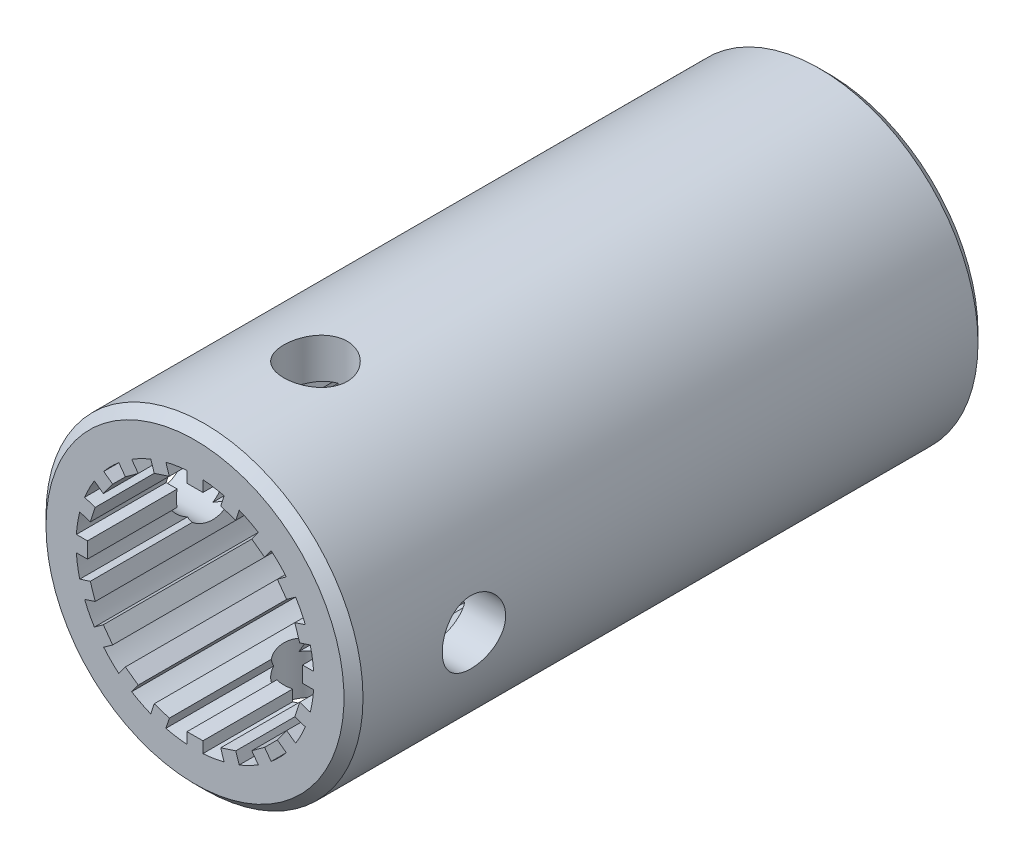
SolidWorks part; units mm, degrees
material "Plain Carbon Steel"
ref_plane "Front Plane" through (0, 0, 0) normal (0, 0, 1) x (1, 0, 0)
ref_plane "Top Plane" through (0, 0, 0) normal (0, 1, 0) x (1, 0, 0)
ref_plane "Right Plane" through (0, 0, 0) normal (1, 0, 0) x (0, 0, -1)
sketch "Sketch1" plane through (0, 0, 0) normal (1, 0, 0) x (0, 0, -1)
  line L0 (-58.8777, 0) -> (63.6887, 0) construction
  line L1 (-25.4, 0) -> (-25.4, 12.7)
  line L2 (-25.4, 12.7) -> (25.4, 12.7)
  line L3 (25.4, 12.7) -> (25.4, 0)
  line L4 (-25.4, 0) -> (25.4, 0)
  point P5 (0, 12.7)
  dimension "D1" = 50.8
  dimension "D2" = 12.7
revolve "Revolve1" add sketch "Sketch1" angle 360 about L0
sketch "Sketch2" plane through (0, 0, 0) normal (0, 1, 0) x (1, 0, 0)
  line L0 (0, 0) -> (0, 50000) construction
  line L1 (-12.7, -25.4) -> (12.7, -25.4) construction
  line L2 (-12.7, -25.4) -> (12.7, -25.4) construction
  circle A0 centre (0, -15.748) radius 2.54
  dimension "D1" = 5.08
  dimension "D2" = 9.652
extrude "Cut-Extrude1" cut sketch "Sketch2" against normal mid plane 34.798
sketch "Sketch3" plane through (0, 0, 0) normal (1, 0, 0) x (0, 0, -1)
  line L0 (0, 0) -> (-50000, 0) construction
  line L1 (-25.4, 12.7) -> (-25.4, -12.7) construction
  line L2 (-25.4, 12.7) -> (-25.4, -12.7) construction
  circle A0 centre (-15.748, 0) radius 2.54
  dimension "D1" = 5.08
  dimension "D2" = 9.652
extrude "Cut-Extrude2" cut sketch "Sketch3" against normal mid plane 34.798
sketch "Sketch4" plane through (0, 0, 25.4) normal (0, 0, 1) x (1, 0, 0)
  line L0 (0, 0) -> (0, 10.781) construction
  line L1 (-0.635, 8.6148) -> (0.635, 8.6148)
  line L2 (0.635, 8.6148) -> (0.635, 9.5038)
  line L3 (-0.635, 8.6148) -> (-0.635, 9.5038)
  line L4 (2.0582, 8.3894) -> (2.3329, 9.2349)
  line L5 (2.0582, 8.3894) -> (3.266, 7.9969)
  line L6 (3.266, 7.9969) -> (3.5408, 8.8424)
  line L7 (4.5499, 7.3428) -> (5.0725, 8.062)
  line L8 (4.5499, 7.3428) -> (5.5774, 6.5963)
  line L9 (5.5774, 6.5963) -> (6.0999, 7.3155)
  line L10 (6.5963, 5.5774) -> (7.3155, 6.0999)
  line L11 (6.5963, 5.5774) -> (7.3428, 4.5499)
  line L12 (7.3428, 4.5499) -> (8.062, 5.0725)
  line L13 (7.9969, 3.266) -> (8.8424, 3.5408)
  line L14 (7.9969, 3.266) -> (8.3894, 2.0582)
  line L15 (8.3894, 2.0582) -> (9.2349, 2.3329)
  line L16 (8.6148, 0.635) -> (9.5038, 0.635)
  line L17 (8.6148, 0.635) -> (8.6148, -0.635)
  line L18 (8.6148, -0.635) -> (9.5038, -0.635)
  line L19 (8.3894, -2.0582) -> (9.2349, -2.3329)
  line L20 (8.3894, -2.0582) -> (7.9969, -3.266)
  line L21 (7.9969, -3.266) -> (8.8424, -3.5408)
  line L22 (7.3428, -4.5499) -> (8.062, -5.0725)
  line L23 (7.3428, -4.5499) -> (6.5963, -5.5774)
  line L24 (6.5963, -5.5774) -> (7.3155, -6.0999)
  line L25 (5.5774, -6.5963) -> (6.0999, -7.3155)
  line L26 (5.5774, -6.5963) -> (4.5499, -7.3428)
  line L27 (4.5499, -7.3428) -> (5.0725, -8.062)
  line L28 (3.266, -7.9969) -> (3.5408, -8.8424)
  line L29 (3.266, -7.9969) -> (2.0582, -8.3894)
  line L30 (2.0582, -8.3894) -> (2.3329, -9.2349)
  line L31 (0.635, -8.6148) -> (0.635, -9.5038)
  line L32 (0.635, -8.6148) -> (-0.635, -8.6148)
  line L33 (-0.635, -8.6148) -> (-0.635, -9.5038)
  line L34 (-2.0582, -8.3894) -> (-2.3329, -9.2349)
  line L35 (-2.0582, -8.3894) -> (-3.266, -7.9969)
  line L36 (-3.266, -7.9969) -> (-3.5408, -8.8424)
  line L37 (-4.5499, -7.3428) -> (-5.0725, -8.062)
  line L38 (-4.5499, -7.3428) -> (-5.5774, -6.5963)
  line L39 (-5.5774, -6.5963) -> (-6.0999, -7.3155)
  line L40 (-6.5963, -5.5774) -> (-7.3155, -6.0999)
  line L41 (-6.5963, -5.5774) -> (-7.3428, -4.5499)
  line L42 (-7.3428, -4.5499) -> (-8.062, -5.0725)
  line L43 (-7.9969, -3.266) -> (-8.8424, -3.5408)
  line L44 (-7.9969, -3.266) -> (-8.3894, -2.0582)
  line L45 (-8.3894, -2.0582) -> (-9.2349, -2.3329)
  line L46 (-8.6148, -0.635) -> (-9.5038, -0.635)
  line L47 (-8.6148, -0.635) -> (-8.6148, 0.635)
  line L48 (-8.6148, 0.635) -> (-9.5038, 0.635)
  line L49 (-8.3894, 2.0582) -> (-9.2349, 2.3329)
  line L50 (-8.3894, 2.0582) -> (-7.9969, 3.266)
  line L51 (-7.9969, 3.266) -> (-8.8424, 3.5408)
  line L52 (-7.3428, 4.5499) -> (-8.062, 5.0725)
  line L53 (-7.3428, 4.5499) -> (-6.5963, 5.5774)
  line L54 (-6.5963, 5.5774) -> (-7.3155, 6.0999)
  line L55 (-5.5774, 6.5963) -> (-6.0999, 7.3155)
  line L56 (-5.5774, 6.5963) -> (-4.5499, 7.3428)
  line L57 (-4.5499, 7.3428) -> (-5.0725, 8.062)
  line L58 (-3.266, 7.9969) -> (-3.5408, 8.8424)
  line L59 (-3.266, 7.9969) -> (-2.0582, 8.3894)
  line L60 (-2.0582, 8.3894) -> (-2.3329, 9.2349)
  arc A0 (-3.5408, 8.8424) -> (-5.0725, 8.062) centre (0, 0) ccw
  arc A1 (-6.0999, 7.3155) -> (-7.3155, 6.0999) centre (0, 0) ccw
  arc A2 (-8.062, 5.0725) -> (-8.8424, 3.5408) centre (0, 0) ccw
  arc A3 (-9.2349, 2.3329) -> (-9.5038, 0.635) centre (0, 0) ccw
  arc A4 (-9.5038, -0.635) -> (-9.2349, -2.3329) centre (0, 0) ccw
  arc A5 (-8.8424, -3.5408) -> (-8.062, -5.0725) centre (0, 0) ccw
  arc A6 (-7.3155, -6.0999) -> (-6.0999, -7.3155) centre (0, 0) ccw
  arc A7 (-5.0725, -8.062) -> (-3.5408, -8.8424) centre (0, 0) ccw
  arc A8 (-2.3329, -9.2349) -> (-0.635, -9.5038) centre (0, 0) ccw
  arc A9 (0.635, -9.5038) -> (2.3329, -9.2349) centre (0, 0) ccw
  arc A10 (3.5408, -8.8424) -> (5.0725, -8.062) centre (0, 0) ccw
  arc A11 (6.0999, -7.3155) -> (7.3155, -6.0999) centre (0, 0) ccw
  arc A12 (8.062, -5.0725) -> (8.8424, -3.5408) centre (0, 0) ccw
  arc A13 (9.2349, -2.3329) -> (9.5038, -0.635) centre (0, 0) ccw
  arc A14 (9.5038, 0.635) -> (9.2349, 2.3329) centre (0, 0) ccw
  arc A15 (8.8424, 3.5408) -> (8.062, 5.0725) centre (0, 0) ccw
  arc A16 (7.3155, 6.0999) -> (6.0999, 7.3155) centre (0, 0) ccw
  arc A17 (5.0725, 8.062) -> (3.5408, 8.8424) centre (0, 0) ccw
  arc A18 (2.3329, 9.2349) -> (0.635, 9.5038) centre (0, 0) ccw
  arc A19 (-0.635, 9.5038) -> (-2.3329, 9.2349) centre (0, 0) ccw
  point P9 (0, 8.6148)
  dimension "D1" = 19.05
  dimension "D2" = 0.635
  dimension "D3" = 0.889
  dimension "D4" = 20
extrude "Cut-Extrude3" cut sketch "Sketch4" against normal blind 21.59
sketch "Sketch5" plane through (0, 0, -25.4) normal (0, 0, -1) x (-1, 0, 0)
  circle A0 centre (0, 0) radius 9.525
  dimension "D1" = 19.05
extrude "Cut-Extrude4" cut sketch "Sketch5" against normal blind 26.67
chamfer "Chamfer1" distance 0.762 angle 45 3 edges at (12.7, 0, 25.4) (-9.525, 0, -25.4) (12.7, 0, -25.4)
